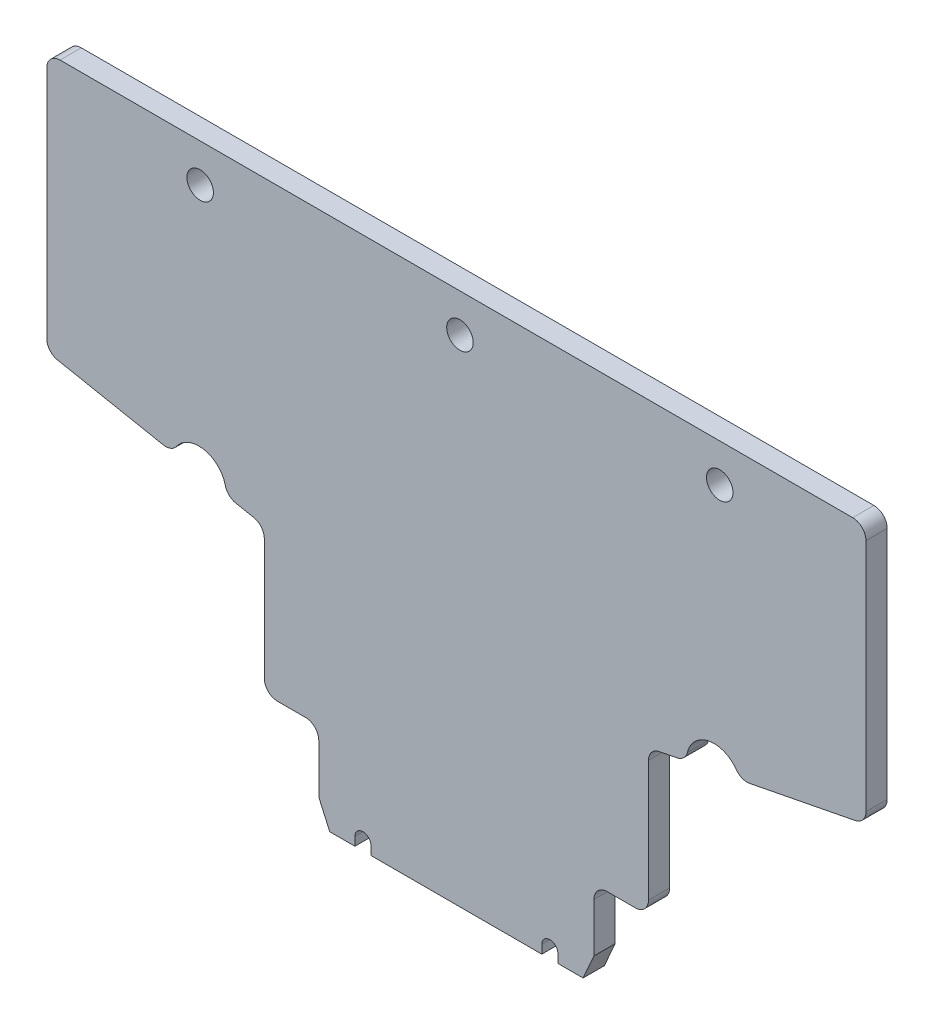
SolidWorks part; units mm, degrees
ref_plane "Front Plane" through (0, 0, 0) normal (0, 0, 1) x (1, 0, 0)
ref_plane "Top Plane" through (0, 0, 0) normal (0, 1, 0) x (1, 0, 0)
ref_plane "Right Plane" through (0, 0, 0) normal (1, 0, 0) x (0, 0, -1)
sketch "Sketch1" plane through (0, 0, 0) normal (0, 0, 1) x (1, 0, 0)
  line L1 (0, 0) -> (80, 0)
  line L2 (0, 0) -> (0, 60)
  line L3 (0, 60) -> (80, 60)
  line L4 (80, 0) -> (80, 60)
  dimension "D1" = 80
  dimension "D2" = 60
extrude "Boss-Extrude1" add sketch "Sketch1" along normal blind 1.6
sketch "Sketch2" plane through (0, 0, 1.6) normal (0, 0, 1) x (1, 0, 0)
  line L0 (8.8305, 49.6486) -> (70.6329, 49.6486)
  line L1 (33.2869, 9.401) -> (46.1765, 9.401)
  line L2 (39.7317, 49.6486) -> (39.7317, 9.401) construction
  line L3 (70.6329, 30.1125) -> (70.6329, 49.6486)
  line L4 (61.1231, 28.2558) -> (70.6329, 30.1125)
  line L5 (54.2244, 26.9088) -> (57.1095, 27.4721)
  line L6 (54.2244, 15.9552) -> (54.2244, 26.9088)
  line L7 (50.1141, 15.9552) -> (54.2244, 15.9552)
  line L8 (50.1141, 11.2565) -> (50.1141, 15.9552)
  line L9 (49.2894, 9.401) -> (50.1141, 11.2565)
  line L10 (47.3899, 9.401) -> (49.2894, 9.401)
  line L11 (47.3899, 10.0478) -> (47.3899, 9.401)
  line L12 (33.2869, 9.401) -> (33.2869, 10.0478)
  line L13 (32.0735, 10.0478) -> (32.0735, 9.401)
  line L14 (32.0735, 9.401) -> (30.174, 9.401)
  line L15 (30.174, 9.401) -> (29.3493, 11.2565)
  line L16 (29.3493, 11.2565) -> (29.3493, 15.9552)
  line L17 (29.3493, 15.9552) -> (25.239, 15.9552)
  line L18 (25.239, 15.9552) -> (25.239, 26.9088)
  line L19 (25.239, 26.9088) -> (22.3539, 27.4721)
  line L20 (18.3403, 28.2558) -> (8.8305, 30.1125)
  line L21 (8.8305, 30.1125) -> (8.8305, 49.6486)
  line L22 (46.1765, 9.401) -> (46.1765, 10.0478)
  arc A0 (57.1095, 27.4721) -> (61.1231, 28.2558) centre (59.1671, 27.6036) cw
  arc A1 (46.1765, 10.0478) -> (47.3899, 10.0478) centre (46.7832, 10.0478) cw
  arc A2 (33.2869, 10.0478) -> (32.0735, 10.0478) centre (32.6802, 10.0478) ccw
  arc A3 (22.3539, 27.4721) -> (18.3403, 28.2558) centre (20.2963, 27.6036) ccw
extrude "Cut-Extrude1" cut sketch "Sketch2" against normal blind 1.6 flip side to cut
fillet "Fillet1" radius 1 14 edges at (29.3493, 15.9552, 0.8) (18.3403, 28.2558, 0.8) (25.239, 26.9088, 0.8) (22.3539, 27.4721, 0.8) (50.1141, 15.9552, 0.8) (54.2244, 15.9552, 0.8) (54.2244, 26.9088, 0.8) (57.1095, 27.4721, 0.8) (61.1231, 28.2558, 0.8) (70.6329, 30.1125, 0.8) (70.6329, 49.6486, 0.8) (8.8305, 49.6486, 0.8) (8.8305, 30.1125, 0.8) (25.239, 15.9552, 0.8)
sketch "Sketch3" plane through (0, 0, 1.6) normal (0, 0, 1) x (1, 0, 0)
  line L0 (69.6329, 49.6486) -> (9.8305, 49.6486) construction
  circle A0 centre (20.4, 46.7686) radius 1
  circle A1 centre (40, 46.7686) radius 1
  circle A2 centre (59.6, 46.7686) radius 1
  dimension "D1" = 2
  dimension "D2" = 19.6
  dimension "D3" = 19.6
  dimension "D4" = 40
  dimension "D5" = 2.88
extrude "Cut-Extrude2" cut sketch "Sketch3" against normal blind 10
